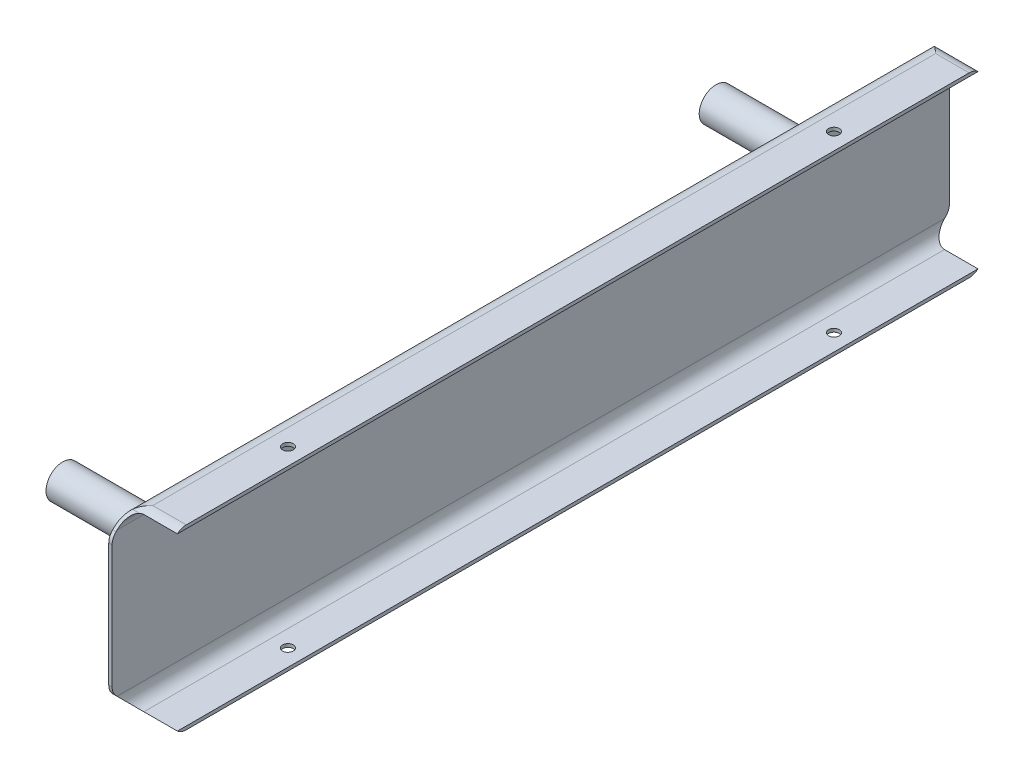
SolidWorks part; units mm, degrees
material "Alliage 1060"
ref_plane "Plan de face" through (0, 0, 0) normal (0, 0, 1) x (1, 0, 0)
ref_plane "Plan de dessus" through (0, 0, 0) normal (0, 1, 0) x (1, 0, 0)
ref_plane "Plan de droite" through (0, 0, 0) normal (1, 0, 0) x (0, 0, -1)
sketch "Esquisse1" plane through (0, 0, 0) normal (0, 0, 1) x (1, 0, 0)
  line L0 (0, 5) -> (0, 48)
  line L1 (5, 53) -> (15, 53)
  line L2 (5, 0) -> (15, 0)
  line L3 (5, 1) -> (15, 1)
  line L4 (1, 5) -> (1, 48)
  line L5 (5, 52) -> (15, 52)
  line L6 (15, 0) -> (15, 1)
  line L7 (15, 53) -> (15, 52)
  arc A0 (0, 5) -> (5, 0) centre (5, 5) ccw
  arc A1 (0, 48) -> (5, 53) centre (5, 48) cw
  arc A2 (1, 5) -> (5, 1) centre (5, 5) ccw
  arc A3 (1, 48) -> (5, 52) centre (5, 48) cw
  point P7 (0, 0)
  point P10 (0, 53)
  dimension "D3" = 5
  dimension "D1" = 15
  dimension "D2" = 53
  dimension "D4" = 1
extrude "Boss.-Extru.1" add sketch "Esquisse1" along normal blind 250
ref_plane "Plan1" through (0, 0, 125) normal (0, 0, -1) x (-1, 0, 0)
sketch "Esquisse5" plane through (0, 0, 0) normal (-1, 0, 0) x (0, 0, 1)
  line L0 (4.6066, 52.5355) -> (0.4645, 48.3934) construction
  line L1 (0, 48) -> (0, 5) construction
  line L2 (0, 8.1421) -> (0, -1)
  line L3 (-1, 44.8579) -> (-1, 8.1421) construction
  line L4 (0.4645, 4.6066) -> (4.6066, 0.4645) construction
  line L5 (250, 0) -> (0, 0) construction
  line L6 (0, 53) -> (0, 48) construction
  line L7 (8.1421, 54) -> (21.0711, 54) construction
  line L9 (21.0711, -1) -> (8.1421, -1) construction
  line L10 (8.1421, 53) -> (21.0711, 53)
  line L11 (5.3137, 51.8284) -> (1.1716, 47.6863)
  line L12 (0, 44.8579) -> (0, 8.1421) construction
  line L13 (1.1716, 5.3137) -> (5.3137, 1.1716)
  line L14 (21.0711, 0) -> (8.1421, 0)
  line L15 (21.0711, 54) -> (21.0711, 53)
  line L16 (21.0711, -1) -> (21.0711, 0)
  line L19 (0, 44.8579) -> (0, 54)
  line L21 (21.0711, 54) -> (0, 54)
  line L22 (0, -1) -> (21.0711, -1)
  arc A0 (4.6066, 52.5355) -> (8.1421, 54) centre (8.1421, 49) cw construction
  arc A1 (0.4645, 48.3934) -> (-1, 44.8579) centre (4, 44.8579) ccw construction
  arc A2 (-1, 8.1421) -> (0.4645, 4.6066) centre (4, 8.1421) ccw construction
  arc A3 (4.6066, 0.4645) -> (8.1421, -1) centre (8.1421, 4) ccw construction
  arc A4 (5.3137, 51.8284) -> (8.1421, 53) centre (8.1421, 49) cw
  arc A5 (1.1716, 47.6863) -> (0, 44.8579) centre (4, 44.8579) ccw
  arc A6 (0, 8.1421) -> (1.1716, 5.3137) centre (4, 8.1421) ccw
  arc A7 (5.3137, 1.1716) -> (8.1421, 0) centre (8.1421, 4) ccw
  point P17 (6.0711, 54)
  point P20 (-1, 46.9289)
  point P23 (-1, 6.0711)
  point P26 (6.0711, -1)
  point P51 (0, 26.5)
  point P52 (0, 26.5)
  dimension "D5" = 5
  dimension "D6" = 5
  dimension "D1" = 45
  dimension "D2" = 45
  dimension "D3" = 10
  dimension "D4" = 10
  dimension "D7" = 53
  dimension "D9" = 15
  dimension "D8" = 1
extrude "Enlèv. mat.-Extru.1" cut sketch "Esquisse5" against normal through all
mirror "Symétrie1" about plane through (0, 0, 125) normal (0, 0, -1) of "Enlèv. mat.-Extru.1"
hole_wizard "Dégagement M31" positions "Esquisse3" profile "Esquisse4" hole size "M3" standard "ISO" end condition through all
sketch "Esquisse3" plane through (0, 53, 0) normal (0, 1, 0) x (1, 0, 0)
  line L3 (15, -125) -> (5, -125) construction
  line L4 (15, -241.8579) -> (15, -8.1421) construction
  line L5 (5, -241.8579) -> (5, -8.1421) construction
  line L7 (10, -206.5) -> (10, -43.5) construction
  point P0 (10, -43.5)
  point P2 (10, -206.5)
  point P30 (10, -125)
  point P31 (10, -125)
  dimension "D1" = 163
sketch "Esquisse4" plane through (10, 53, 43.5) normal (1, 0, 0) x (0, 0, 1)
  line L0 (0, 0) -> (0, 53)
  line L1 (0, 53) -> (1.6, 53)
  line L2 (1.6, 53) -> (1.6, 0)
  line L5 (1.6, 0) -> (0, 0)
  line L11 (0, -6.35) -> (0, 107.95) construction
  dimension "Diamètre du perçage jusqu'au prochain" = 3.2
  dimension "Profondeur du perçage jusqu'au prochain" = 53
sketch "Esquisse6" plane through (0, 0, 0) normal (-1, 0, 0) x (0, 0, 1)
  line L0 (125, 48) -> (125, 5) construction
  line L1 (248.5147, 48) -> (1.4853, 48) construction
  line L2 (248.5147, 5) -> (1.4853, 5) construction
  line L3 (0, 44.8579) -> (0, 8.1421) construction
  circle A0 centre (27.5, 26.5) radius 5
  circle A1 centre (222.5, 26.5) radius 5
  point P12 (0, 26.5)
  dimension "D1" = 10
  dimension "D3" = 195
extrude "Boss.-Extru.2" add sketch "Esquisse6" along normal blind 41.23
